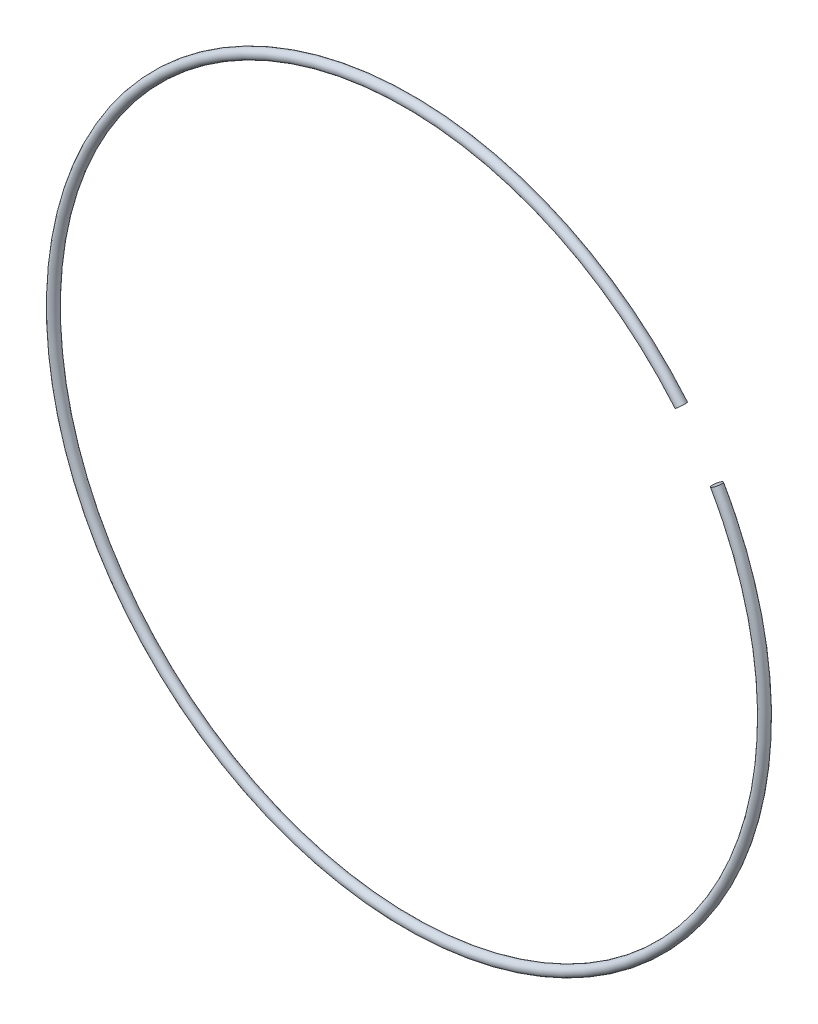
SolidWorks part; units mm, degrees
ref_plane "Front Plane" through (0, 0, 0) normal (0, 0, 1) x (1, 0, 0)
ref_plane "Top Plane" through (0, 0, 0) normal (0, 1, 0) x (1, 0, 0)
ref_plane "Right Plane" through (0, 0, 0) normal (1, 0, 0) x (0, 0, -1)
sketch "Sketch1" plane through (0, 0, 0) normal (0, 0, 1) x (1, 0, 0)
  line L0 (0, 0) -> (87.5589, 73.4706) construction
  line L1 (0, 0) -> (98.9867, 57.15) construction
  line L2 (0, 0) -> (0, 114.3) construction
  arc A0 (87.5589, 73.4706) -> (98.9867, 57.15) centre (0, 0) ccw
  dimension "D1" = 228.6
  dimension "D2" = 10
  dimension "D3" = 50
ref_plane "Plane1" through (87.5589, 73.4706, 0) normal (-0.6428, 0.766, 0) x (0.766, 0.6428, 0)
sketch "Sketch2" plane through (87.5589, 73.4706, 0) normal (-0.6428, 0.766, 0) x (0.766, 0.6428, 0)
  circle A0 centre (0, 0) radius 1.5875
  dimension "D1" = 3.175
sweep "Sweep1" add profiles "Sketch2" path "Sketch1"
